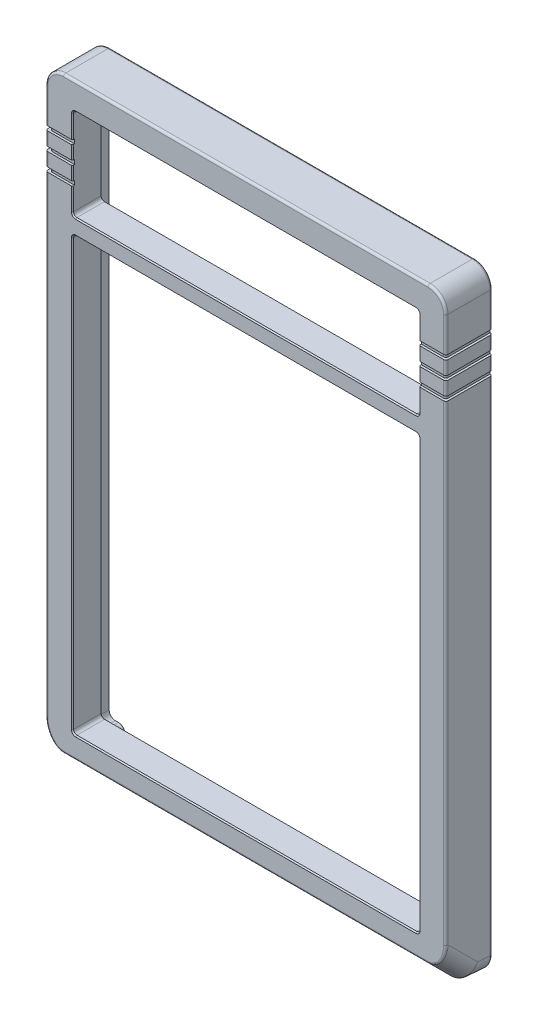
SolidWorks part; units mm, degrees
ref_plane "前视基准面" through (0, 0, 0) normal (0, 0, 1) x (1, 0, 0)
ref_plane "上视基准面" through (0, 0, 0) normal (0, 1, 0) x (1, 0, 0)
ref_plane "右视基准面" through (0, 0, 0) normal (1, 0, 0) x (0, 0, -1)
sketch "草图1" plane through (0, 0, 0) normal (1, 0, 0) x (0, 0, -1)
  line L0 (0, 0) -> (0, 137)
  line L1 (0, 137) -> (-11.4, 137)
  line L2 (-11.4, 137) -> (-11.4, 5.7169)
  line L3 (-11.4, 5.7169) -> (-6.1321, 0.449)
  line L5 (-11.4, 5.7169) -> (6.3075, 5.7169) construction
  line L6 (0, 0) -> (-5.7899, 0) construction
  line L7 (0, 0) -> (-1, 0)
  line L8 (-6.1321, 0.449) -> (-1, 0)
  dimension "D1" = 11.4
  dimension "D2" = 137
  dimension "D3" = 45
  dimension "D4" = 5
  dimension "D5" = 1
  dimension "D6" = 7.45
extrude "凸台-拉伸1" add sketch "草图1" along normal blind 89.5
sketch "草图2" plane through (0, 0, 0) normal (0, 0, -1) x (-1, 0, 0)
  line L0 (0, 0) -> (0, 137) construction
  line L1 (-87.9, 135.4) -> (-1.6, 135.4)
  line L2 (-87.9, 135.4) -> (-87.9, 1.5)
  line L3 (-87.9, 1.5) -> (-1.6, 1.5)
  line L4 (-1.6, 135.4) -> (-1.6, 1.5)
  line L5 (-89.5, 137) -> (0, 137) construction
  line L6 (-89.5, 0) -> (-89.5, 137) construction
  line L7 (-89.5, 0) -> (0, 0) construction
  dimension "D1" = 1.6
  dimension "D2" = 1.6
  dimension "D3" = 1.6
  dimension "D4" = 1.5
extrude "切除-拉伸1" cut sketch "草图2" against normal blind 1 flip side to cut
sketch "草图5" plane through (0, 0, 0) normal (0, 0, -1) x (-1, 0, 0)
  line L0 (-102.6154, 68.5) -> (30.5586, 68.5) construction
  line L1 (-89.5, 0) -> (0, 0) construction
  line L3 (-89.5, 0) -> (-89.5, 137) construction
  line L4 (0, 0) -> (0, 137) construction
  line L5 (0, 137) -> (-89.5, 137) construction
  circle A0 centre (-84.95, 4.55) radius 0.9
  circle A1 centre (-4.55, 4.55) radius 0.9
  circle A2 centre (-4.55, 132.45) radius 0.9
  circle A3 centre (-84.95, 132.45) radius 0.9
  dimension "D1" = 1.8
  dimension "D2" = 4.55
  dimension "D3" = 4.55
  dimension "D4" = 4.55
  dimension "D5" = 4.55
extrude "切除-拉伸3" cut sketch "草图5" against normal blind 6
sketch "草图6" plane through (0, 0, 0) normal (0, 0, -1) x (-1, 0, 0)
  line L0 (-83.2, 2.7) -> (-6.3, 2.7)
  line L1 (-2.8, 70.55) -> (-2.8, 6.2)
  line L2 (-2.8, 70.55) -> (-2.8, 130.7)
  line L3 (-83.2, 134.2) -> (-6.3, 134.2)
  line L4 (-86.7, 130.7) -> (-86.7, 74.35)
  line L5 (-86.7, 74.35) -> (-86.7, 6.2)
  line L6 (-1.6, 1.5) -> (-1.6, 135.4) construction
  line L7 (-87.9, 1.5) -> (-1.6, 1.5) construction
  line L8 (-87.9, 135.4) -> (-87.9, 1.5) construction
  line L9 (-1.6, 135.4) -> (-87.9, 135.4) construction
  line L10 (-83.2, 2.7) -> (-83.2, 6.2)
  line L11 (-83.2, 6.2) -> (-86.7, 6.2)
  line L12 (-6.3, 2.7) -> (-6.3, 6.2)
  line L13 (-6.3, 6.2) -> (-2.8, 6.2)
  line L17 (-6.3, 134.2) -> (-6.3, 130.7)
  line L18 (-6.3, 130.7) -> (-2.8, 130.7)
  line L19 (-86.7, 130.7) -> (-83.2, 130.7)
  line L20 (-83.2, 130.7) -> (-83.2, 134.2)
  dimension "D1" = 1.2
  dimension "D2" = 1.2
  dimension "D3" = 1.2
  dimension "D4" = 1.2
  dimension "D5" = 4.7
extrude "切除-拉伸4" cut sketch "草图6" against normal blind 5
fillet "圆角1" radius 1.4 8 edges at (86.7, 6.2, 2.5) (83.2, 2.7, 2.5) (2.8, 6.2, 2.5) (6.3, 2.7, 2.5) (2.8, 130.7, 2.5) (6.3, 134.2, 2.5) (86.7, 130.7, 2.5) (83.2, 134.2, 2.5)
fillet "圆角2" radius 1.4 4 edges at (6.3, 6.2, 2.5) (83.2, 6.2, 2.5) (6.3, 130.7, 2.5) (83.2, 130.7, 2.5)
sketch "草图3" plane through (0, 0, 0) normal (0, 0, -1) x (-1, 0, 0)
  line L0 (-44.75, 159.1782) -> (-44.75, -24.9782) construction
  line L1 (0, 137) -> (-89.5, 137) construction
  line L2 (-83.5, 106.95) -> (-6, 106.95)
  line L3 (-83.5, 106.95) -> (-83.5, 10.25)
  line L4 (-83.5, 10.25) -> (-6, 10.25)
  line L5 (-6, 106.95) -> (-6, 10.25)
  line L6 (-83.5, 106.95) -> (-6, 10.25) construction
  line L7 (-83.5, 10.25) -> (-6, 106.95) construction
  line L8 (-89.5, 0) -> (0, 0) construction
  line L9 (-83.5, 131) -> (-6, 131)
  line L10 (-83.5, 131) -> (-83.5, 110.5)
  line L11 (-83.5, 110.5) -> (-6, 110.5)
  line L12 (-6, 131) -> (-6, 110.5)
  point P2 (-44.75, 58.6)
  dimension "D1" = 77.5
  dimension "D2" = 10.25
  dimension "D3" = 96.7
  dimension "D4" = 6
  dimension "D5" = 20.5
extrude "切除-拉伸2" cut sketch "草图3" against normal up to surface (11.4 mm away) up to face at (44.75, 71.3585, 11.4)
fillet "圆角9" radius 0.75 8 edges at (83.5, 106.95, 8.2) (6, 106.95, 8.2) (6, 10.25, 8.2) (83.5, 10.25, 8.2) (6, 131, 8.2) (83.5, 131, 8.2) (6, 110.5, 8.2) (83.5, 110.5, 8.2)
fillet "圆角4" radius 4 6 edges at (89.5, 3.083, 8.766) (89.5, 0.2245, 3.566) (0, 3.083, 8.766) (0, 0.2245, 3.566) (0, 137, 6.2) (89.5, 137, 6.2)
fillet "圆角7" radius 2.2 4 edges at (1.6, 1.5, 0.5) (87.9, 1.5, 0.5) (1.6, 135.4, 0.5) (87.9, 135.4, 0.5)
fillet "圆角8" radius 0.5 27 edges at (88.3284, 1.5789, 5.6052) (1.1716, 1.5789, 5.6052) (88.3284, 135.8284, 11.4) (89.5, 72.1869, 11.4) (88.3284, 7.3738, 11.4) (44.75, 5.7169, 11.4) (1.1716, 7.3738, 11.4) (0, 72.1869, 11.4) (1.1716, 135.8284, 11.4) (1.1716, 135.8284, 1) (0, 68.5076, 1) (1.1716, 1.176, 1) (44.75, 0, 1) (88.3284, 1.176, 1) (89.5, 68.5076, 1) (88.3284, 135.8284, 1) (2.2444, 134.7556, 0) (1.6, 68.45, 0) (2.2444, 2.1444, 0) (44.75, 1.5, 0) (87.2556, 2.1444, 0) (87.9, 68.45, 0) (87.2556, 134.7556, 0) (44.75, 0.449, 6.1321) (44.75, 137, 11.4) (44.75, 137, 1) (44.75, 135.4, 0)
chamfer "倒角1" distance 0.25 angle 45 16 edges at (44.75, 10.25, 11.4) (83.5, 58.6, 11.4) (6, 58.6, 11.4) (44.75, 106.95, 11.4) (83.2803, 10.4697, 11.4) (6.2197, 10.4697, 11.4) (83.2803, 106.7303, 11.4) (6.2197, 106.7303, 11.4) (83.2803, 110.7197, 11.4) (83.5, 120.75, 11.4) (83.2803, 130.7803, 11.4) (44.75, 131, 11.4) (6.2197, 130.7803, 11.4) (44.75, 110.5, 11.4) (6.2197, 110.7197, 11.4) (6, 120.75, 11.4)
sketch "草图7" plane through (0, 0, 11.4) normal (0, 0, 1) x (1, 0, 0)
  line L0 (95.3844, 120.75) -> (-7.2026, 120.75)
  line L1 (93.3171, 124.75) -> (-6, 124.75)
  line L2 (93.3171, 116.75) -> (-4.4, 116.75)
  point P8 (0, 0)
  dimension "D1" = 4
extrude "切除-拉伸-薄壁1" cut sketch "草图7" against normal blind 0.5 thin thin type mid plane wall 1
sketch "草图8" plane through (89.5, 0, 0) normal (1, 0, 0) x (0, 0, -1)
  line L0 (-14.7436, 120.75) -> (0.3077, 120.75) construction
  line L2 (-14.4559, 124.75) -> (0, 124.75)
  line L3 (0, 133.2) -> (0, 3.7) construction
  line L4 (-14.4559, 116.75) -> (-0.5, 116.75)
  line L5 (-0.5, 3.7) -> (-0.5, 133.2) construction
  line L6 (-14.4559, 120.75) -> (0.672, 120.75)
  dimension "D1" = 4
extrude "切除-拉伸-薄壁2" cut sketch "草图8" against normal blind 0.5 thin thin type mid plane wall 1
sketch "草图9" plane through (0, 0, 0) normal (-1, 0, 0) x (0, 0, 1)
  line L0 (12.2607, 120.75) -> (-2.117, 120.75) construction
  line L1 (12.385, 124.75) -> (-1.164, 124.75)
  line L2 (12.385, 116.75) -> (-1.164, 116.75)
  line L3 (-1.164, 120.75) -> (12.2607, 120.75)
  dimension "D1" = 4
extrude "切除-拉伸-薄壁3" cut sketch "草图9" against normal blind 0.5 thin thin type mid plane wall 1
fillet "圆角10" radius 0.5 6 edges at (89, 116.75, 10.9) (89, 120.75, 10.9) (89, 124.75, 10.9) (0.5, 116.75, 10.9) (0.5, 120.75, 10.9) (0.5, 124.75, 10.9)
